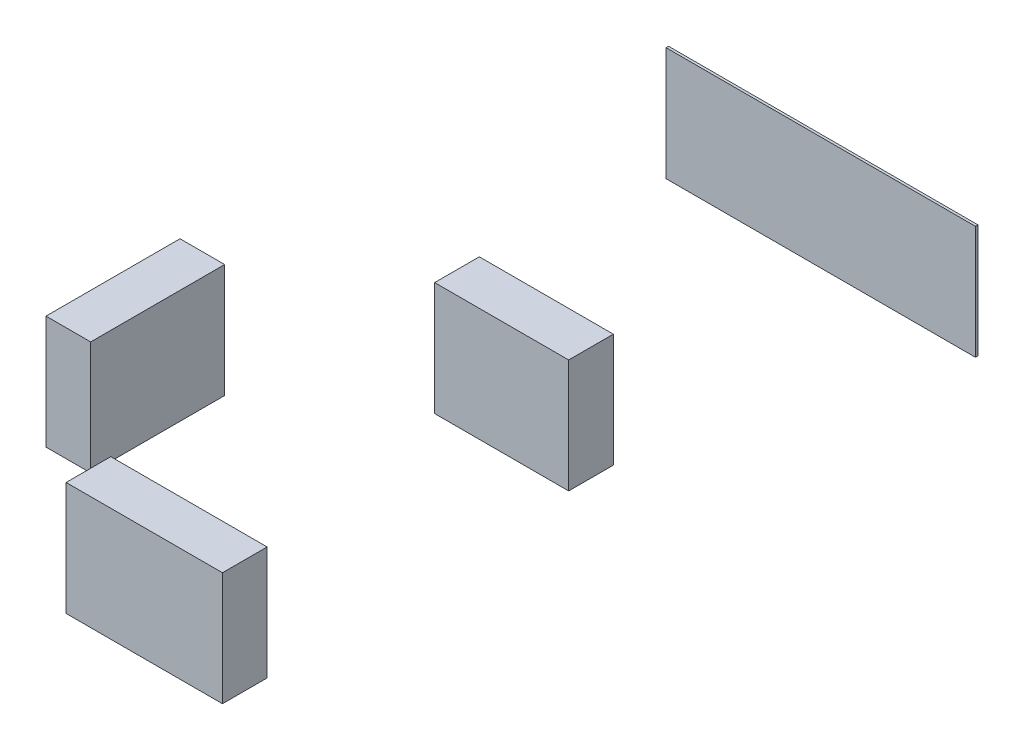
SolidWorks part; units mm, degrees
ref_plane "Front Plane" through (0, 0, 0) normal (0, 0, 1) x (1, 0, 0)
ref_plane "Top Plane" through (0, 0, 0) normal (0, 1, 0) x (1, 0, 0)
ref_plane "Right Plane" through (0, 0, 0) normal (1, 0, 0) x (0, 0, -1)
sketch "Sketch1" plane through (0, 0, 0) normal (0, 1, 0) x (1, 0, 0)
  line L0 (4.7, 0) -> (0, 0) construction
  line L1 (2.95, 1) -> (6.45, 1)
  line L2 (2.95, 1) -> (2.95, 0)
  line L3 (2.95, 0) -> (6.45, 0)
  line L4 (6.45, 1) -> (6.45, 0)
  line L5 (-0.5, 6) -> (0.5, 6)
  line L6 (-0.5, 6) -> (-0.5, 3)
  line L7 (-0.5, 3) -> (0.5, 3)
  line L8 (0.5, 6) -> (0.5, 3)
  line L9 (3.2, 9) -> (6.2, 9)
  line L10 (3.2, 9) -> (3.2, 8)
  line L11 (3.2, 8) -> (6.2, 8)
  line L12 (6.2, 9) -> (6.2, 8)
  line L13 (0, 0) -> (0, 3) construction
  line L14 (0, 6) -> (0, 9) construction
  line L15 (0, 9) -> (4.7, 9) construction
  line L16 (1.2368, 15.2) -> (8.1632, 15.2)
  line L17 (-0.5, 4.5) -> (-3.7242, 4.5) construction
  line L18 (4.7, 9) -> (4.7, 15.2) construction
  line L19 (8.1632, 15.2) -> (8.1632, 15.1441)
  line L20 (8.1632, 15.1441) -> (1.2368, 15.1441)
  line L21 (1.2368, 15.1441) -> (1.2368, 15.2)
  point P16 (0, 3)
  point P20 (4.7, 9)
  dimension "D2" = 3.5
  dimension "D3" = 1
  dimension "D4" = 3
  dimension "D7" = 4.7
  dimension "D8" = 3
  dimension "D9" = 4.7
  dimension "D10" = 10.7
extrude "Boss-Extrude1" add sketch "Sketch1" along normal blind 2.54
